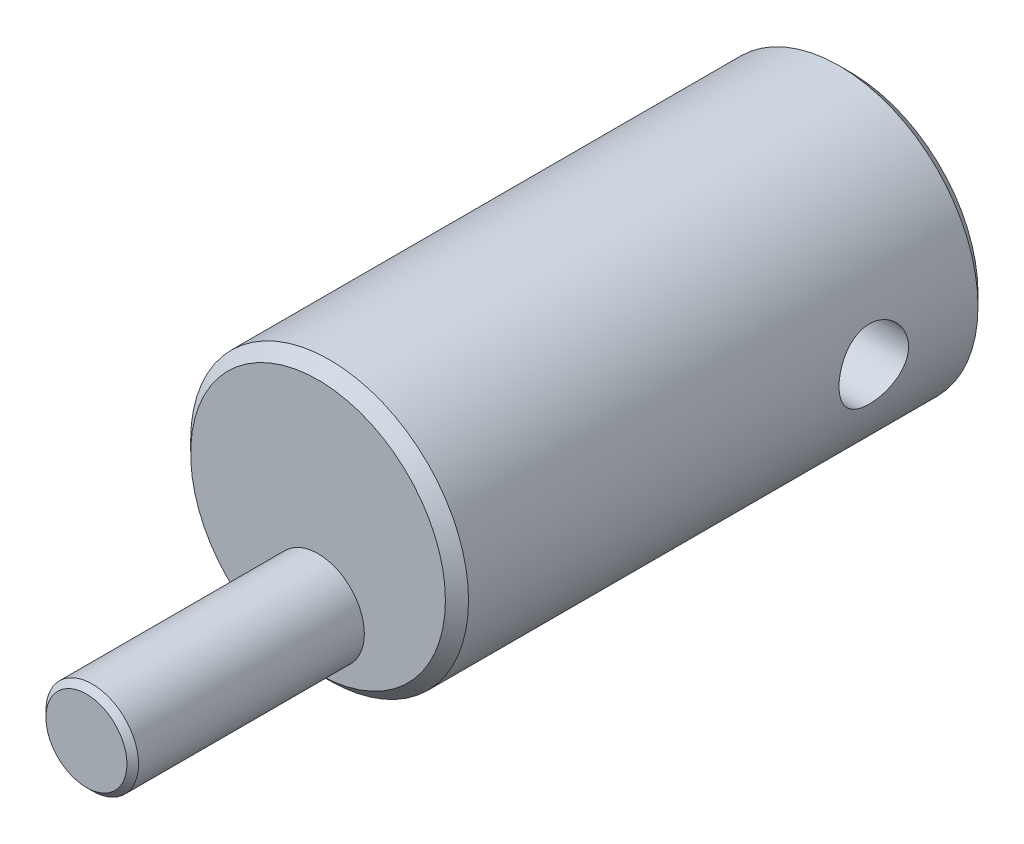
SolidWorks part; units mm, degrees
ref_plane "Front Plane" through (0, 0, 0) normal (0, 0, 1) x (1, 0, 0)
ref_plane "Top Plane" through (0, 0, 0) normal (0, 1, 0) x (1, 0, 0)
ref_plane "Right Plane" through (0, 0, 0) normal (1, 0, 0) x (0, 0, -1)
sketch "Sketch1" plane through (0, 0, 0) normal (0, 0, 1) x (1, 0, 0)
  circle A0 centre (0, 0) radius 6
  dimension "D1" = 12
extrude "Boss-Extrude1" add sketch "Sketch1" along normal blind 23
sketch "Sketch2" plane through (0, 0, 23) normal (0, 0, 1) x (1, 0, 0)
  circle A0 centre (0, -3) radius 2
  dimension "D2" = 4
  dimension "D1" = 3
extrude "Boss-Extrude2" add sketch "Sketch2" along normal blind 10
chamfer "Chamfer1" distance 0.5 angle 45 2 edges at (6, 0, 23) (6, 0, 0)
chamfer "Chamfer2" distance 0.25 angle 45 1 edges at (2, -3, 33)
sketch "Sketch3" plane through (0, 0, 0) normal (1, 0, 0) x (0, 0, -1)
  circle A0 centre (-5, 0) radius 1.5
  dimension "D2" = 3
  dimension "D1" = 5
extrude "Cut-Extrude1" cut sketch "Sketch3" against normal through all both and the other way through all
